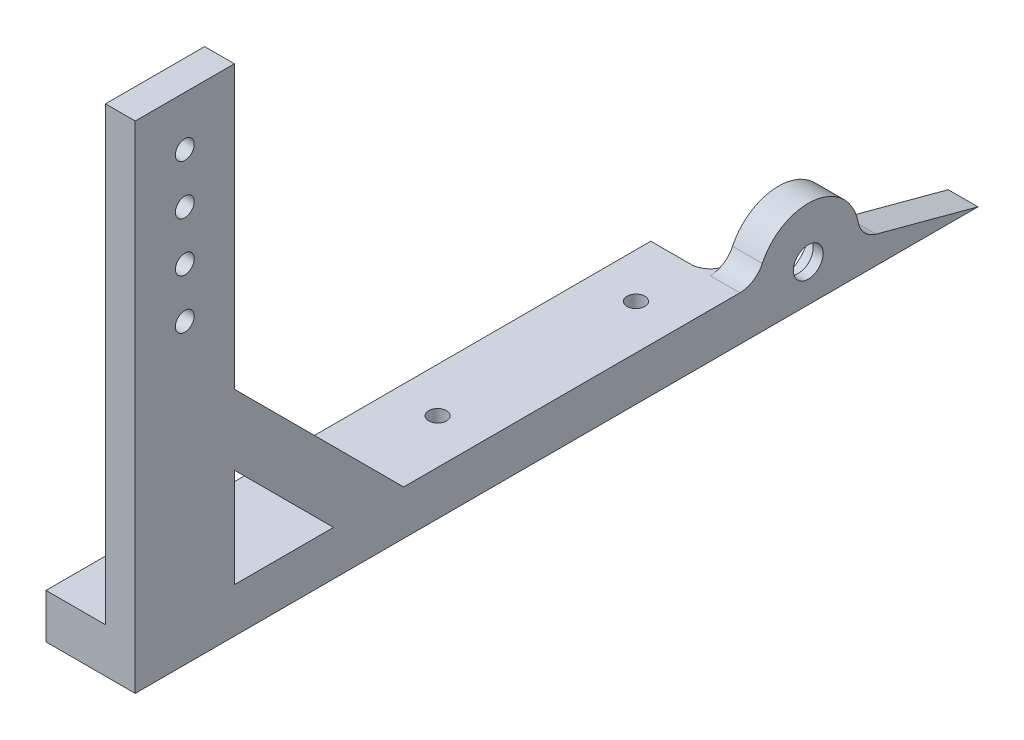
SolidWorks part; units mm, degrees
ref_plane "Front Plane" through (0, 0, 0) normal (0, 0, 1) x (1, 0, 0)
ref_plane "Top Plane" through (0, 0, 0) normal (0, 1, 0) x (1, 0, 0)
ref_plane "Right Plane" through (0, 0, 0) normal (1, 0, 0) x (0, 0, -1)
sketch "Sketch1" plane through (0, 0, 0) normal (1, 0, 0) x (0, 0, -1)
  line L0 (0, 0) -> (127, 0)
  line L1 (127, 0) -> (100.9008, 6.9932)
  line L2 (0, 11.43) -> (65.9946, 11.43)
  line L3 (0, 11.43) -> (0, 0) construction
  line L4 (0, 11.43) -> (-63.5, 11.43)
  line L5 (-88.9, 127) -> (-88.9, 0)
  line L6 (-88.9, 0) -> (0, 0)
  line L7 (-76.2, 127) -> (-76.2, 0) construction
  line L8 (65.6713, 22.86) -> (83.5147, 9.525) construction
  line L10 (-88.9, 127) -> (-63.5, 127)
  line L11 (-63.5, 11.43) -> (-63.5, 127)
  circle A0 centre (83.5147, 9.525) radius 7.9375
  arc A1 (96.3051, 11.9459) -> (71.7389, 15.0734) centre (83.5147, 9.525) ccw
  circle A2 centre (83.5147, 9.525) radius 6.35 construction
  arc A3 (71.7389, 15.0734) -> (65.9946, 11.43) centre (65.9946, 17.78) cw
  arc A4 (96.3051, 11.9459) -> (100.9008, 6.9932) centre (102.5443, 13.1269) ccw
  circle A5 centre (-76.2, 114.3) radius 2.413
  circle A6 centre (-76.2, 88.9) radius 2.413
  circle A7 centre (-76.2, 101.6) radius 2.413
  circle A8 centre (-76.2, 76.2) radius 2.413
  circle A9 centre (65.6713, 22.86) radius 3.175 construction
  circle A10 centre (65.6713, 22.86) radius 9.525 construction
  point P6 (83.5147, 1.5875)
  dimension "D1" = 15.875
  dimension "D2" = 1.5875
  dimension "D3" = 5.08
  dimension "D7" = 12.7
  dimension "D8" = 6.35
  dimension "D9" = 6.35
  dimension "D13" = 4.826
  dimension "D15" = 25.4
  dimension "D17" = 12.7
  dimension "D18" = 11.9459
  dimension "D19" = 6.35
  dimension "D22" = 6.35
  dimension "D4" = 127
  dimension "D5" = 15
  dimension "D6" = 11.43
  dimension "D10" = 215.9
  dimension "D11" = 25.4
  dimension "D12" = 127
  dimension "D14" = 12.7
  dimension "D16" = 12.7
  dimension "D20" = 22.2758
  dimension "D21" = 22.86
extrude "Boss-Extrude1" add sketch "Sketch1" along normal blind 7.62
sketch "Sketch2" plane through (7.62, 0, 0) normal (1, 0, 0) x (0, 0, -1)
  circle A0 centre (83.5147, 9.525) radius 7.9375 construction
  circle A1 centre (83.5147, 9.525) radius 3.81
  circle A2 centre (83.5147, 9.525) radius 7.9375
  dimension "D1" = 7.62
extrude "Boss-Extrude2" add sketch "Sketch2" against normal blind 2.54
sketch "Sketch3" plane through (0, 0, 0) normal (-1, 0, 0) x (0, 0, 1)
  line L0 (88.9, 0) -> (-127, 0) construction
  line L1 (88.9, 11.43) -> (-66.04, 11.43)
  line L2 (88.9, 11.43) -> (88.9, 0)
  line L3 (88.9, 0) -> (-66.04, 0)
  line L4 (-66.04, 11.43) -> (-66.04, 0)
  line L5 (88.9, 0) -> (-127, 0) construction
  line L6 (88.9, 127) -> (88.9, 0) construction
  line L9 (-65.9946, 11.43) -> (63.5, 11.43) construction
  dimension "D1" = 154.94
extrude "Boss-Extrude3" add sketch "Sketch3" along normal blind 15.24
fillet "Fillet1" radius 5.08 1 edges
sketch "Sketch4" plane through (7.62, 0, 0) normal (1, 0, 0) x (0, 0, -1)
  line L0 (-63.5, 54.7905) -> (-20.1395, 11.43)
  line L1 (-63.5, 11.43) -> (-63.5, 127) construction
  line L2 (65.9946, 11.43) -> (-63.5, 11.43) construction
  line L3 (-63.5, 36.83) -> (-38.1, 11.43)
  line L4 (-63.5, 54.7905) -> (-63.5, 36.83)
  line L5 (-38.1, 11.43) -> (-20.1395, 11.43)
  dimension "D1" = 12.7
  dimension "D2" = 45
  dimension "D3" = 25.4
extrude "Boss-Extrude4" add sketch "Sketch4" against normal up to surface (7.62 mm away) up to face at (0, 76.2, 73.787)
sketch "Sketch5" plane through (0, 0, 0) normal (0, -1, 0) x (1, 0, 0)
  line L0 (7.62, -127) -> (-15.24, -127) construction
  line L1 (-15.24, -127) -> (-15.24, -66.04) construction
  line L2 (-3.81, -127) -> (-3.81, -50.8) construction
  circle A0 centre (-3.81, -50.8) radius 2.286
  circle A1 centre (-3.81, 0) radius 2.286
  dimension "D2" = 4.572
  dimension "D1" = 76.2
  dimension "D3" = 2
extrude "Cut-Extrude1" cut sketch "Sketch5" against normal through all
sketch "Sketch6" plane through (0, 0, 0) normal (0, -1, 0) x (1, 0, 0)
  line L0 (7.62, -127) -> (0, -127) construction
  line L1 (1.6159, -50.8) -> (-1.097, -46.101)
  line L2 (-1.097, -46.101) -> (-6.523, -46.101)
  line L3 (-6.523, -46.101) -> (-9.2359, -50.8)
  line L4 (-9.2359, -50.8) -> (-6.523, -55.499)
  line L5 (-6.523, -55.499) -> (-1.097, -55.499)
  line L6 (-1.097, -55.499) -> (1.6159, -50.8)
  line L7 (-1.097, -4.699) -> (1.6159, 0)
  line L8 (1.6159, 0) -> (-1.097, 4.699)
  line L9 (-1.097, 4.699) -> (-6.523, 4.699)
  line L10 (-6.523, 4.699) -> (-9.2359, 0)
  line L11 (-9.2359, 0) -> (-6.523, -4.699)
  line L12 (-6.523, -4.699) -> (-1.097, -4.699)
  circle A0 centre (-3.81, -50.8) radius 4.699 construction
  circle A1 centre (-3.81, 0) radius 4.699 construction
  dimension "D1" = 9.398
extrude "Cut-Extrude2" cut sketch "Sketch6" against normal blind 6.35
